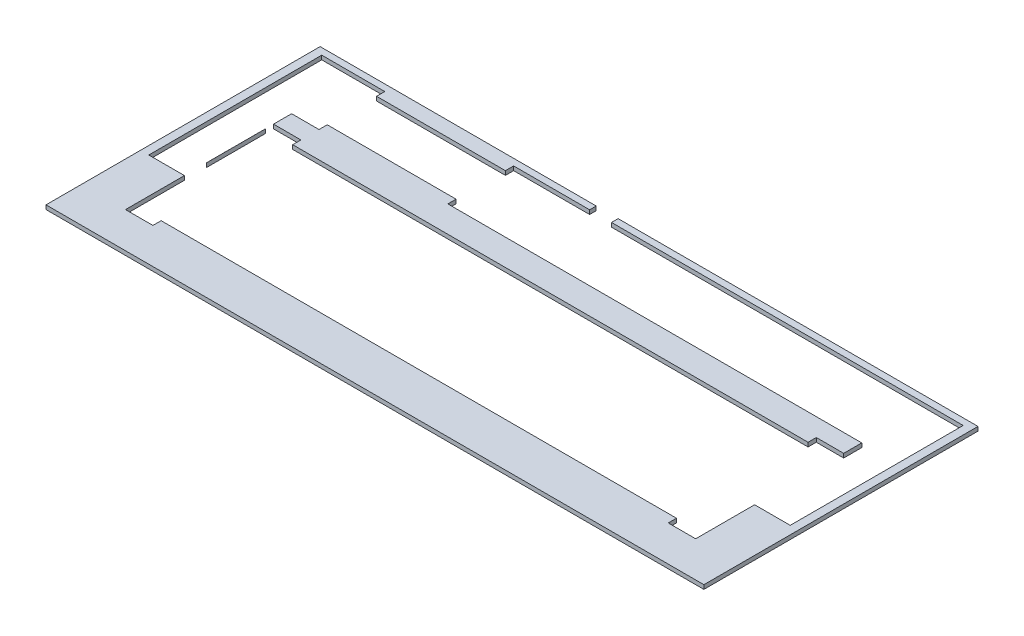
SolidWorks part; units mm, degrees
other "Marca1"
sketch "Croquis6" plane through (483.1, 12, 3.1) normal (0.4175, 0.3737, 0.8283) x (0.8528, 0.1536, -0.4991)
material "Balsa"
ref_plane "Alzado" through (0, 0, 0) normal (0, 0, 1) x (1, 0, 0)
ref_plane "Planta" through (0, 0, 0) normal (0, 1, 0) x (1, 0, 0)
ref_plane "Vista lateral" through (0, 0, 0) normal (1, 0, 0) x (0, 0, -1)
sketch "Croquis1" plane through (0, 0, 0) normal (0, 1, 0) x (1, 0, 0)
  line L0 (0, 0) -> (-3.1, 0) construction
  line L1 (0, 0) -> (480, 0)
  line L2 (0, 0) -> (0, 200)
  line L3 (0, 200) -> (480, 200)
  line L4 (480, 0) -> (480, 200)
  line L5 (0, 0) -> (0, -3.1) construction
  line L6 (-3.1, 0) -> (-3.1, -3.1) construction
  line L7 (-3.1, -3.1) -> (0, -3.1) construction
  line L8 (480, 200) -> (480, 203.1) construction
  line L9 (480, 203.1) -> (483.1, 203.1) construction
  line L11 (-3.1, -3.1) -> (483.1, -3.1)
  line L12 (-3.1, -3.1) -> (-3.1, 203.1)
  line L13 (-3.1, 203.1) -> (483.1, 203.1)
  line L14 (483.1, -3.1) -> (483.1, 203.1)
extrude "Saliente-Extruir1" add sketch "Croquis1" along normal blind 12 contours L1 L4 L3 L2 | L11 L14 L13 L12 L4 L1 L2 L3
sketch "Croquis2" plane through (0, 12, 0) normal (0, 1, 0) x (1, 0, 0)
  line L0 (21.9636, 184.1902) -> (21.9636, 179.1902) construction
  line L1 (17, 184.1902) -> (17, 189.1902) construction
  line L2 (17, 189.1902) -> (16, 189.1902)
  line L3 (28, 184.1902) -> (58, 184.1902) construction
  line L4 (32, 128) -> (448, 128)
  line L6 (32, 32) -> (448, 32)
  line L8 (32, 128) -> (448, 32) construction
  line L9 (32, 32) -> (448, 128) construction
  line L10 (32, 80) -> (17, 80) construction
  line L15 (17, 184.1902) -> (12, 184.1902) construction
  line L16 (28, 184.1902) -> (17, 184.1902) construction
  line L17 (17, 184.1902) -> (17, 80) construction
  line L18 (17, 184.1902) -> (17, 149.1902) construction
  line L19 (12, 185.1902) -> (12, 184.1902)
  line L20 (12, 146.1902) -> (12, 184.1902)
  line L21 (463, 189.1902) -> (464, 189.1902)
  line L22 (17, 80) -> (12, 80) construction
  line L23 (17, 80) -> (17, 75) construction
  line L24 (12, 184.1902) -> (12, 80)
  line L25 (12, 80) -> (12, 78)
  line L26 (15, 75) -> (17, 75)
  line L27 (17, 75) -> (32, 75)
  line L28 (17, 80) -> (21.9636, 80) construction
  line L29 (468, 185.1902) -> (468, 79)
  line L30 (31.9636, 85) -> (32, 85)
  line L31 (463, 189.1902) -> (448, 189.1902)
  line L32 (21.9636, 95) -> (21.9636, 175.1902)
  line L33 (25.9636, 179.1902) -> (28, 179.1902)
  line L34 (58, 184.1902) -> (448, 184.1902) construction
  line L35 (448, 80) -> (463, 80) construction
  line L36 (463, 80) -> (463, 184.1902) construction
  line L37 (463, 184.1902) -> (448, 184.1902) construction
  line L38 (459, 75) -> (459, 85) construction
  line L39 (448.8054, 85) -> (448, 85)
  line L40 (459, 75) -> (448, 75)
  line L41 (458.8036, 95.1927) -> (458.0364, 135)
  line L42 (32, 179.1902) -> (32, 189.1902) construction
  line L43 (448.0364, 125) -> (448, 125)
  line L44 (32, 189.1902) -> (17, 189.1902)
  line L45 (458.0364, 135) -> (458.0364, 169.1902)
  line L46 (464, 75) -> (459, 75)
  line L47 (166, 189.1902) -> (448, 189.1902)
  line L48 (32, 189.1902) -> (166, 189.1902)
  line L50 (32, 153.1902) -> (166, 153.1902)
  line L52 (448.0364, 179.1902) -> (170, 179.1902)
  line L53 (166, 175.1902) -> (166, 153.1902)
  line L54 (32, 175.1902) -> (32, 153.1902)
  line L55 (32, 128) -> (32, 85)
  line L56 (32, 75) -> (32, 32)
  line L57 (32, 85) -> (32, 75)
  line L58 (448, 128) -> (448, 85)
  line L59 (448, 32) -> (448, 75)
  line L60 (448, 85) -> (448, 75)
  line L61 (201.4487, 189.1902) -> (201.4487, 203.1)
  line L62 (-3.1, 203.1) -> (483.1, 203.1) construction
  line L63 (201.4487, 203.1) -> (217.4247, 203.1)
  line L64 (217.4247, 203.1) -> (217.4247, 189.1902)
  arc A0 (458.8036, 95.1927) -> (448.8054, 85) centre (448.8054, 95) cw
  arc A1 (458.0364, 169.1902) -> (448.0364, 179.1902) centre (448.0364, 169.1902) ccw
  arc A2 (21.9636, 95) -> (31.9636, 85) centre (31.9636, 95) ccw
  arc A3 (16, 189.1902) -> (12, 185.1902) centre (16, 185.1902) ccw
  arc A4 (464, 189.1902) -> (468, 185.1902) centre (464, 185.1902) cw
  arc A5 (468, 79) -> (464, 75) centre (464, 79) cw
  arc A6 (170, 179.1902) -> (166, 175.1902) centre (170, 175.1902) ccw
  arc A7 (12, 78) -> (15, 75) centre (15, 78) ccw
  arc A8 (21.9636, 175.1902) -> (25.9636, 179.1902) centre (25.9636, 175.1902) cw
  arc A9 (28, 179.1902) -> (32, 175.1902) centre (28, 175.1902) cw
  point P6 (240, 80)
  dimension "D1" = 10
  dimension "D2" = 4
  dimension "D3" = 4
sketch "Croquis3" plane through (0, 12, 0) normal (0, 1, 0) x (1, 0, 0)
  line L1 (0, 0) -> (480, 0)
  line L2 (0, 0) -> (0, 200)
  line L3 (0, 200) -> (480, 200)
  line L4 (480, 0) -> (480, 200)
  line L5 (-3.1, -3.1) -> (483.1, -3.1)
  line L6 (-3.1, -3.1) -> (-3.1, 203.1)
  line L7 (-3.1, 203.1) -> (483.1, 203.1)
  line L8 (483.1, -3.1) -> (483.1, 203.1)
extrude "Cortar-Extruir1" cut sketch "Croquis3" against normal blind 5
extrude "Cortar-Extruir3" cut sketch "Croquis2" against normal blind 8
sketch "Croquis4" plane through (0, 12, 0) normal (0, 1, 0) x (1, 0, 0)
  line L0 (32, 128) -> (32, 134)
  line L1 (32, 134) -> (52, 134)
  line L2 (52, 134) -> (52, 128)
  line L3 (32, 128) -> (448, 128) construction
  line L4 (52, 128) -> (32, 128)
  line L5 (240, 32) -> (240, 128) construction
  line L6 (32, 32) -> (448, 32) construction
  line L7 (32, 128) -> (448, 128) construction
  line L8 (240, 80) -> (282.8706, 80) construction
  line L9 (428, 134) -> (428, 128)
  line L10 (448, 128) -> (448, 134)
  line L11 (428, 128) -> (448, 128)
  line L12 (448, 134) -> (428, 134)
  line L13 (448, 32) -> (448, 26)
  line L14 (428, 32) -> (448, 32)
  line L15 (448, 26) -> (428, 26)
  line L16 (428, 26) -> (428, 32)
  line L17 (52, 26) -> (52, 32)
  line L18 (52, 32) -> (32, 32)
  line L19 (32, 26) -> (52, 26)
  line L20 (32, 32) -> (32, 26)
  line L21 (32, 75) -> (32, 69)
  line L22 (32, 75) -> (32, 32) construction
  line L23 (12, 80) -> (6, 80) construction
  line L24 (12, 185.1902) -> (12, 78) construction
  line L25 (32, 69) -> (6, 69)
  line L26 (16, 189.1902) -> (16, 195.1902) construction
  line L27 (6, 69) -> (6, 80)
  line L28 (6, 80) -> (6, 195.1902)
  line L29 (6, 195.1902) -> (16, 195.1902)
  line L30 (32, 189.1902) -> (32, 195.1902)
  line L31 (16, 189.1902) -> (201.4487, 189.1902) construction
  line L32 (32, 195.1902) -> (16, 195.1902)
  line L33 (16, 189.1902) -> (32, 189.1902)
  line L34 (12, 185.1902) -> (12, 80)
  line L35 (32, 75) -> (15, 75)
  line L36 (12, 80) -> (12, 78)
  line L37 (31.9636, 85) -> (32, 128)
  line L38 (32, 175.1902) -> (32, 134)
  line L39 (25.9636, 179.1902) -> (28, 179.1902)
  line L40 (21.9636, 175.1902) -> (21.9636, 95)
  line L41 (99, 153.1902) -> (99, 189.1902) construction
  line L42 (32, 153.1902) -> (52, 153.1902)
  line L43 (32, 153.1902) -> (32, 147.1902)
  line L44 (32, 147.1902) -> (52, 147.1902)
  line L45 (52, 153.1902) -> (52, 147.1902)
  line L46 (32, 153.1902) -> (166, 153.1902) construction
  line L47 (99, 171.1902) -> (116.5825, 171.1902) construction
  line L48 (52, 189.1902) -> (52, 195.1902)
  line L49 (32, 195.1902) -> (52, 195.1902)
  line L50 (32, 189.1902) -> (52, 189.1902)
  line L51 (146, 189.1902) -> (146, 195.1902)
  line L52 (166, 189.1902) -> (146, 189.1902)
  line L53 (166, 195.1902) -> (146, 195.1902)
  line L54 (166, 189.1902) -> (166, 195.1902)
  line L55 (166, 153.1902) -> (146, 153.1902)
  line L56 (166, 153.1902) -> (166, 147.1902)
  line L57 (146, 153.1902) -> (146, 147.1902)
  line L58 (166, 147.1902) -> (146, 147.1902)
  line L59 (468, 185.1902) -> (474, 185.1902) construction
  line L60 (464, 189.1902) -> (464, 195.1902) construction
  line L61 (464, 195.1902) -> (474, 195.1902) construction
  line L62 (166, 147.1902) -> (474, 147.1902) construction
  line L63 (448, 75) -> (448, 69) construction
  line L64 (166, 195.1902) -> (474, 195.1902)
  line L65 (166, 195.1902) -> (166, 147.1902)
  line L66 (166, 147.1902) -> (474, 147.1902)
  line L67 (474, 195.1902) -> (474, 147.1902)
  line L68 (448, 75) -> (448, 32) construction
  line L70 (474, 147.1902) -> (448, 147.1902)
  line L71 (474, 147.1902) -> (474, 69)
  line L72 (474, 69) -> (448, 69)
  line L73 (448, 147.1902) -> (448, 69)
  arc A0 (16, 189.1902) -> (12, 185.1902) centre (16, 185.1902) ccw
  arc A1 (12, 78) -> (15, 75) centre (15, 78) ccw
  arc A2 (21.9636, 95) -> (31.9636, 85) centre (31.9636, 95) ccw construction
  arc A3 (28, 179.1902) -> (32, 175.1902) centre (28, 175.1902) cw
  arc A4 (21.9636, 175.1902) -> (25.9636, 179.1902) centre (25.9636, 175.1902) cw
  arc A5 (21.9636, 95) -> (31.9636, 85) centre (31.9636, 95) ccw
  line M14 (32, 128) -> (448, 128)
  line M15 (448, 128) -> (448, 85)
  line M16 (448, 85) -> (448.8054, 85)
  arc M17 (448.8054, 85) -> (458.8036, 95.1927) centre (448.8054, 95) ccw
  line M18 (458.8036, 95.1927) -> (458.0364, 135)
  line M19 (458.0364, 135) -> (458.0364, 169.1902)
  arc M20 (458.0364, 169.1902) -> (448.0364, 179.1902) centre (448.0364, 169.1902) ccw
  line M21 (448.0364, 179.1902) -> (170, 179.1902)
  arc M22 (170, 179.1902) -> (166, 175.1902) centre (170, 175.1902) ccw
  line M23 (166, 175.1902) -> (166, 153.1902)
  line M24 (166, 153.1902) -> (32, 153.1902)
  line M25 (32, 153.1902) -> (32, 175.1902)
  arc M26 (32, 175.1902) -> (28, 179.1902) centre (28, 175.1902) ccw
  line M27 (28, 179.1902) -> (25.9636, 179.1902)
  arc M28 (25.9636, 179.1902) -> (21.9636, 175.1902) centre (25.9636, 175.1902) ccw
  line M29 (21.9636, 175.1902) -> (21.9636, 95)
  arc M30 (21.9636, 95) -> (31.9636, 85) centre (31.9636, 95) ccw
extrude "Cortar-Extruir4" cut sketch "Croquis4" against normal blind 3 contours L38 L37 L0 M25 M26 M27 M28 M29 M30 | L2 L1 L0 M14 | L45 L38 L44 M24 | A1 L36 L34 A0 L33 L30 L32 L29 L28 L27 L25 L21 L35 | L30 L50 L48 L49 | L18 L20 L19 L17 | L52 L54 L53 L51 | L58 L56 L57 M24 | L56 L66 M19 M20 M21 M22 M23 | L67 L64 L54 L65 L66 M22 M21 M20 M19 | L73 L72 L71 L66 M16 M19 M18 M17 | L10 L12 L9 M14 | L16 L15 L13 L14 | L66 L73 L10 M15 M16 M17 M18 M19
sketch "Croquis5" plane through (0, 4, 0) normal (0, 1, 0) x (1, 0, 0)
  line L0 (32.046, 84.9265) -> (32, 75)
  line L2 (32, 75) -> (15, 75)
  line L3 (25.9636, 179.1902) -> (28, 179.1902)
  line L4 (21.9636, 175.1902) -> (21.9636, 95)
  line L5 (32, 175.1902) -> (32, 153.1902)
  line L6 (32, 153.1902) -> (166, 153.1902)
  line L7 (166, 153.1902) -> (166, 175.1902)
  line L8 (170, 179.1902) -> (448.0364, 179.1902)
  line L9 (458.0364, 169.1902) -> (458.8036, 95.1927)
  line L10 (448.8054, 85) -> (448, 85)
  line L11 (448, 85) -> (448, 75)
  line L12 (448, 75) -> (464, 75)
  line L13 (468, 79) -> (468, 185.1902)
  line L14 (468, 185.1902) -> (468, 79) construction
  line L15 (464, 189.1902) -> (217.4247, 189.1902)
  line L16 (217.4247, 189.1902) -> (217.4247, 203.1)
  line L17 (217.4247, 203.1) -> (201.4487, 203.1)
  line L18 (201.4487, 203.1) -> (201.4487, 189.1902)
  line L19 (201.4487, 189.1902) -> (16, 189.1902)
  line L20 (12, 185.1902) -> (12, 78)
  arc A1 (12, 78) -> (15, 75) centre (15, 78) ccw
  arc A2 (25.9636, 179.1902) -> (21.9636, 175.1902) centre (25.9636, 175.1902) ccw
  arc A3 (21.9636, 95) -> (32.046, 84.9265) centre (32.0371, 95) ccw
  arc A4 (28, 179.1902) -> (32, 175.1902) centre (28, 175.1902) cw
  arc A5 (166, 175.1902) -> (170, 179.1902) centre (170, 175.1902) cw
  arc A6 (448.0364, 179.1902) -> (458.0364, 169.1902) centre (448.0364, 169.1902) cw
  arc A7 (448.8054, 85) -> (458.8036, 95.1927) centre (448.7156, 95.0881) ccw
  arc A8 (468, 79) -> (464, 75) centre (464, 79) cw
  arc A9 (468, 185.1902) -> (464, 189.1902) centre (464, 185.1902) ccw construction
  arc A10 (464, 189.1902) -> (468, 185.1902) centre (464, 185.1902) cw
  arc A11 (16, 189.1902) -> (12, 185.1902) centre (16, 185.1902) ccw
extrude "Cortar-Extruir5" cut sketch "Croquis5" against normal blind 2
sketch "Croquis7" plane through (0, 2, 0) normal (0, 1, 0) x (1, 0, 0)
  line L1 (-211.6054, 341.1803) -> (510.3417, 341.1803)
  line L2 (-211.6054, 341.1803) -> (-211.6054, -18.2396)
  line L3 (-211.6054, -18.2396) -> (510.3417, -18.2396)
  line L4 (510.3417, 341.1803) -> (510.3417, -18.2396)
  line L5 (-211.6054, 341.1803) -> (510.3417, -18.2396) construction
  line L6 (-211.6054, -18.2396) -> (510.3417, 341.1803) construction
  point P0 (149.3682, 161.4704)
extrude "Cortar-Extruir6" cut sketch "Croquis7" against normal blind 10
sketch "Croquis8" plane through (0, 4, 0) normal (0, 1, 0) x (1, 0, 0)
  line L1 (32, 128) -> (448, 128)
  line L2 (32, 128) -> (32, 32)
  line L3 (32, 32) -> (448, 32)
  line L4 (448, 128) -> (448, 32)
extrude "Cortar-Extruir7" cut sketch "Croquis8" against normal blind 10
sketch "Croquis9" plane through (0, 9, 0) normal (0, 1, 0) x (1, 0, 0)
  line L1 (512.9567, 229.5955) -> (-18.948, 229.5955)
  line L2 (512.9567, 229.5955) -> (512.9567, -16.7579)
  line L3 (512.9567, -16.7579) -> (-18.948, -16.7579)
  line L4 (-18.948, 229.5955) -> (-18.948, -16.7579)
  point P4 (425.7612, 15.2567)
  point P5 (512.9567, 229.5955)
extrude "Cortar-Extruir8" cut sketch "Croquis9" against normal blind 10
